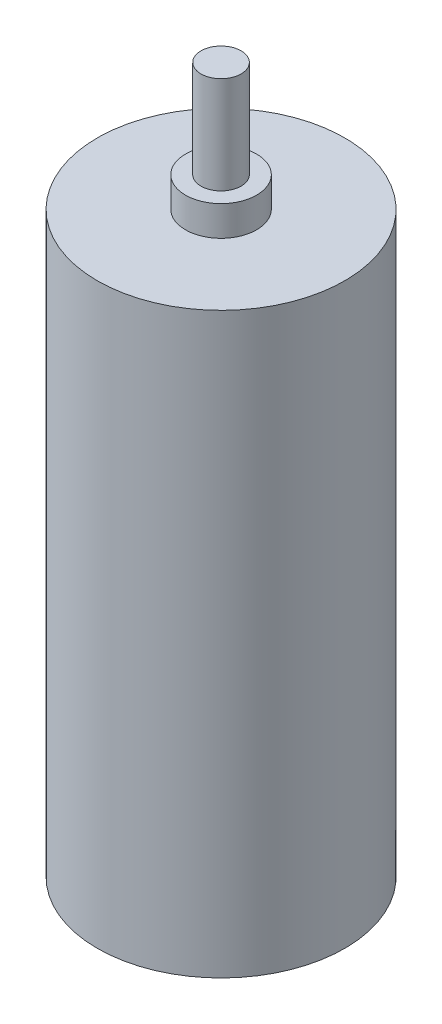
SolidWorks part; units mm, degrees
ref_plane "Front Plane" through (0, 0, 0) normal (0, 0, 1) x (1, 0, 0)
ref_plane "Top Plane" through (0, 0, 0) normal (0, 1, 0) x (1, 0, 0)
ref_plane "Right Plane" through (0, 0, 0) normal (1, 0, 0) x (0, 0, -1)
sketch "Sketch1" plane through (0, 0, 0) normal (0, 1, 0) x (1, 0, 0)
  circle A0 centre (0, 0) radius 12.35
  dimension "D1" = 24.7
extrude "Boss-Extrude1" add sketch "Sketch1" along normal blind 57.7
sketch "Sketch2" plane through (0, 57.7, 0) normal (0, 1, 0) x (1, 0, 0)
  circle A0 centre (0, 0) radius 3.55
  dimension "D1" = 7.1
extrude "Boss-Extrude2" add sketch "Sketch2" along normal blind 3
sketch "Sketch3" plane through (0, 60.7, 0) normal (0, 1, 0) x (1, 0, 0)
  circle A0 centre (0, 0) radius 2
  dimension "D1" = 4
extrude "Boss-Extrude3" add sketch "Sketch3" along normal blind 9.7
sketch "Sketch4" plane through (0, 57.7, 0) normal (0, 1, 0) x (1, 0, 0)
  circle A0 centre (0, 8.85) radius 2
  circle A1 centre (0, 0) radius 12.35 construction
  circle A2 centre (0, -8.9) radius 2
  dimension "D2" = 4
  dimension "D4" = 4
  dimension "D1" = 8.85
  dimension "D3" = 8.9
